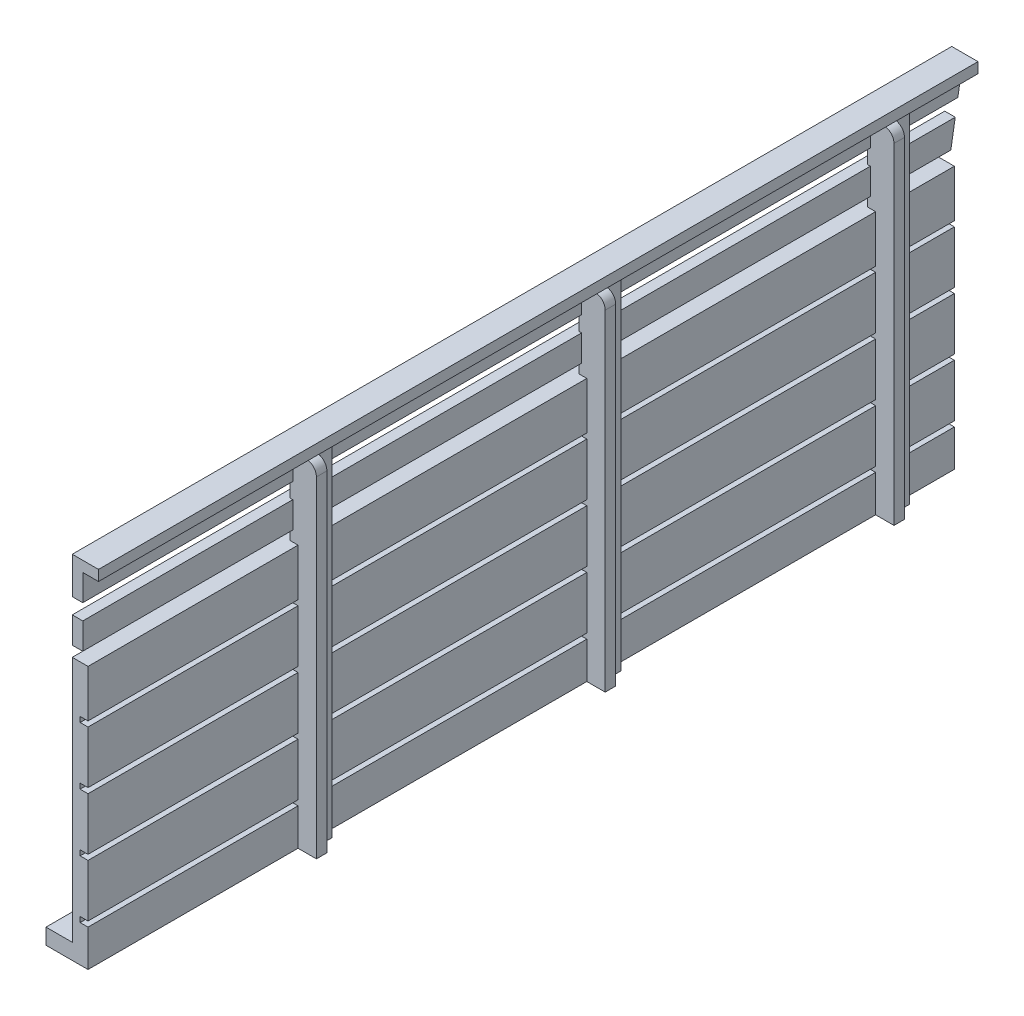
SolidWorks part; units mm, degrees
ref_plane "Front Plane" through (0, 0, 0) normal (0, 0, 1) x (1, 0, 0)
ref_plane "Top Plane" through (0, 0, 0) normal (0, 1, 0) x (1, 0, 0)
ref_plane "Right Plane" through (0, 0, 0) normal (1, 0, 0) x (0, 0, -1)
sketch "Sketch1" plane through (0, 0, 0) normal (1, 0, 0) x (0, 0, -1)
  line L1 (-82.5, 25) -> (82.5, 25)
  line L2 (-82.5, 25) -> (-82.5, -25)
  line L3 (-82.5, -25) -> (82.5, -25)
  line L4 (82.5, 25) -> (82.5, -25)
  line L5 (-82.5, 25) -> (82.5, -25) construction
  line L6 (-82.5, -25) -> (82.5, 25) construction
  point P0 (0, 0)
  dimension "D1" = 50
  dimension "D2" = 165
extrude "Boss-Extrude1" add sketch "Sketch1" along normal blind 3
sketch "Sketch3" plane through (3, 0, 0) normal (1, 0, 0) x (0, 0, -1)
  line L0 (-82.5, 25) -> (-82.5, -25) construction
  line L1 (-82.5, -17) -> (82.5, -17)
  line L2 (-82.5, -17) -> (-82.5, -18)
  line L3 (-82.5, -18) -> (82.5, -18)
  line L4 (82.5, -17) -> (82.5, -18)
  line L5 (82.5, -25) -> (82.5, 25) construction
  line L6 (-82.5, -25) -> (82.5, -25) construction
  line L7 (82.5, 25) -> (-82.5, 25) construction
  line L8 (-82.5, -6) -> (82.5, -6)
  line L9 (-82.5, -6) -> (-82.5, -7)
  line L10 (-82.5, -7) -> (82.5, -7)
  line L11 (82.5, -6) -> (82.5, -7)
  line L12 (-82.5, 5) -> (82.5, 5)
  line L13 (-82.5, 5) -> (-82.5, 4)
  line L14 (-82.5, 4) -> (82.5, 4)
  line L15 (82.5, 5) -> (82.5, 4)
  line L16 (-82.5, 16) -> (82.5, 16)
  line L17 (-82.5, 16) -> (-82.5, 15)
  line L18 (-82.5, 15) -> (82.5, 15)
  line L19 (82.5, 16) -> (82.5, 15)
  dimension "D1" = 1
  dimension "D2" = 7
  dimension "D3" = 1
  dimension "D4" = 10
  dimension "D5" = 1
  dimension "D6" = 10
  dimension "D7" = 1
  dimension "D8" = 10
  dimension "D9" = 9
extrude "Cut-Extrude1" cut sketch "Sketch3" against normal blind 1.5
sketch "Sketch4" plane through (3, 0, 0) normal (1, 0, 0) x (0, 0, -1)
  line L0 (-82.5, -25) -> (82.5, -25) construction
  line L1 (-42.5, -25) -> (-37.5, -25)
  line L2 (-42.5, -25) -> (-42.5, 40)
  line L3 (-42.5, 40) -> (-37.5, 40)
  line L4 (-37.5, -25) -> (-37.5, 40)
  line L5 (-82.5, -7) -> (-82.5, -17) construction
  line L7 (12.5, -25) -> (17.5, -25)
  line L8 (12.5, -25) -> (12.5, 40)
  line L9 (12.5, 40) -> (17.5, 40)
  line L10 (17.5, -25) -> (17.5, 40)
  line L11 (67.5, -25) -> (72.5, -25)
  line L12 (67.5, -25) -> (67.5, 40)
  line L13 (67.5, 40) -> (72.5, 40)
  line L14 (72.5, -25) -> (72.5, 40)
  dimension "D1" = 65
  dimension "D2" = 5
  dimension "D3" = 40
  dimension "D4" = 5
  dimension "D5" = 65
  dimension "D6" = 50
  dimension "D7" = 5
  dimension "D8" = 50
  dimension "D9" = 65
extrude "Boss-Extrude2" add sketch "Sketch4" along normal mid plane 3
sketch "Sketch5" plane through (4.5, 0, 0) normal (1, 0, 0) x (0, 0, -1)
  line L0 (-37.5, 40) -> (-42.5, 40) construction
  line L1 (-42.5, -25) -> (-40.5, -25)
  line L2 (-42.5, -25) -> (-42.5, 40)
  line L3 (-42.5, 40) -> (-40.5, 40)
  line L4 (-40.5, -25) -> (-40.5, 40)
  line L5 (17.5, 40) -> (12.5, 40) construction
  line L6 (12.5, -25) -> (14.5, -25)
  line L7 (12.5, -25) -> (12.5, 40)
  line L8 (12.5, 40) -> (14.5, 40)
  line L9 (14.5, -25) -> (14.5, 40)
  line L10 (72.5, 40) -> (67.5, 40) construction
  line L11 (67.5, -25) -> (69.5, -25)
  line L12 (67.5, -25) -> (67.5, 40)
  line L13 (67.5, 40) -> (69.5, 40)
  line L14 (69.5, -25) -> (69.5, 40)
  dimension "D1" = 2
  dimension "D2" = 65
  dimension "D3" = 2
  dimension "D4" = 65
  dimension "D5" = 2
extrude "Boss-Extrude3" add sketch "Sketch5" along normal blind 2
fillet "Fillet1" radius 2 3 edges at (6.5, 40, -68.5) (6.5, 40, -13.5) (6.5, 40, 41.5)
sketch "Sketch6" plane through (0, 40, 0) normal (0, 1, 0) x (1, 0, 0)
  line L1 (0, -82.5) -> (5, -82.5)
  line L2 (0, -82.5) -> (0, 85)
  line L3 (0, 85) -> (5, 85)
  line L4 (5, -82.5) -> (5, 85)
  dimension "D1" = 167.5
  dimension "D2" = 5
sketch "Sketch8" plane through (0, 0, 0) normal (-1, 0, 0) x (0, 0, 1)
  line L0 (82.5, -25) -> (82.5, 40) construction
  line L1 (82.5, 40) -> (-85, 40) construction
  line L2 (-82.5, 25) -> (82.5, 25) construction
  line L8 (82.5, 35) -> (-85, 35)
  line L9 (82.5, 35) -> (82.5, 40)
  line L10 (82.5, 40) -> (-85, 40)
  line L11 (-85, 35) -> (-85, 40)
  line L12 (82.5, 27) -> (-85, 27)
  line L13 (82.5, 27) -> (82.5, 32)
  line L14 (82.5, 32) -> (-85, 32)
  line L15 (-85, 27) -> (-85, 32)
  dimension "D1" = 5
  dimension "D2" = 3
  dimension "D3" = 2
  dimension "D4" = 5
  dimension "D6" = 167.5
extrude "Boss-Extrude4" add sketch "Sketch8" against normal blind 2
extrude "Boss-Extrude5" add sketch "Sketch6" along normal blind 2
sketch "Sketch9" plane through (3, 0, 0) normal (1, 0, 0) x (0, 0, -1)
  line L0 (82.5, 25) -> (82.5, 44.094) construction
  line L5 (82.5, 25) -> (85, 40)
  line L6 (85, 40) -> (86.8234, 40)
  line L7 (86.8234, 40) -> (86.8234, 25)
  line L8 (86.8234, 25) -> (82.5, 25)
extrude "Cut-Extrude2" cut sketch "Sketch9" against normal up to surface (3 mm away) up to face at (0, 38.5, -1.25)
sketch "Sketch10" plane through (0, 0, 0) normal (-1, 0, 0) x (0, 0, 1)
  line L0 (82.5, 25) -> (82.5, -25) construction
  line L1 (-82.5, -25) -> (82.5, -25)
  line L2 (-82.5, -25) -> (-82.5, -22)
  line L3 (-82.5, -22) -> (82.5, -22)
  line L4 (82.5, -25) -> (82.5, -22)
  dimension "D1" = 3
extrude "Boss-Extrude6" add sketch "Sketch10" along normal blind 5
sketch "Sketch11" plane through (0, -22, 0) normal (0, 1, 0) x (1, 0, 0)
  line L0 (-5, -82.5) -> (-5, 82.5) construction
  line L1 (0, 82.5) -> (-5, 82.5)
  line L2 (0, 82.5) -> (0, 79.5)
  line L3 (0, 79.5) -> (-5, 79.5)
  line L4 (-5, 82.5) -> (-5, 79.5)
  dimension "D1" = 3
extrude "Cut-Extrude3" cut sketch "Sketch11" against normal up to surface (3 mm away) up to face at (3.6364, -25, -12.1364)
